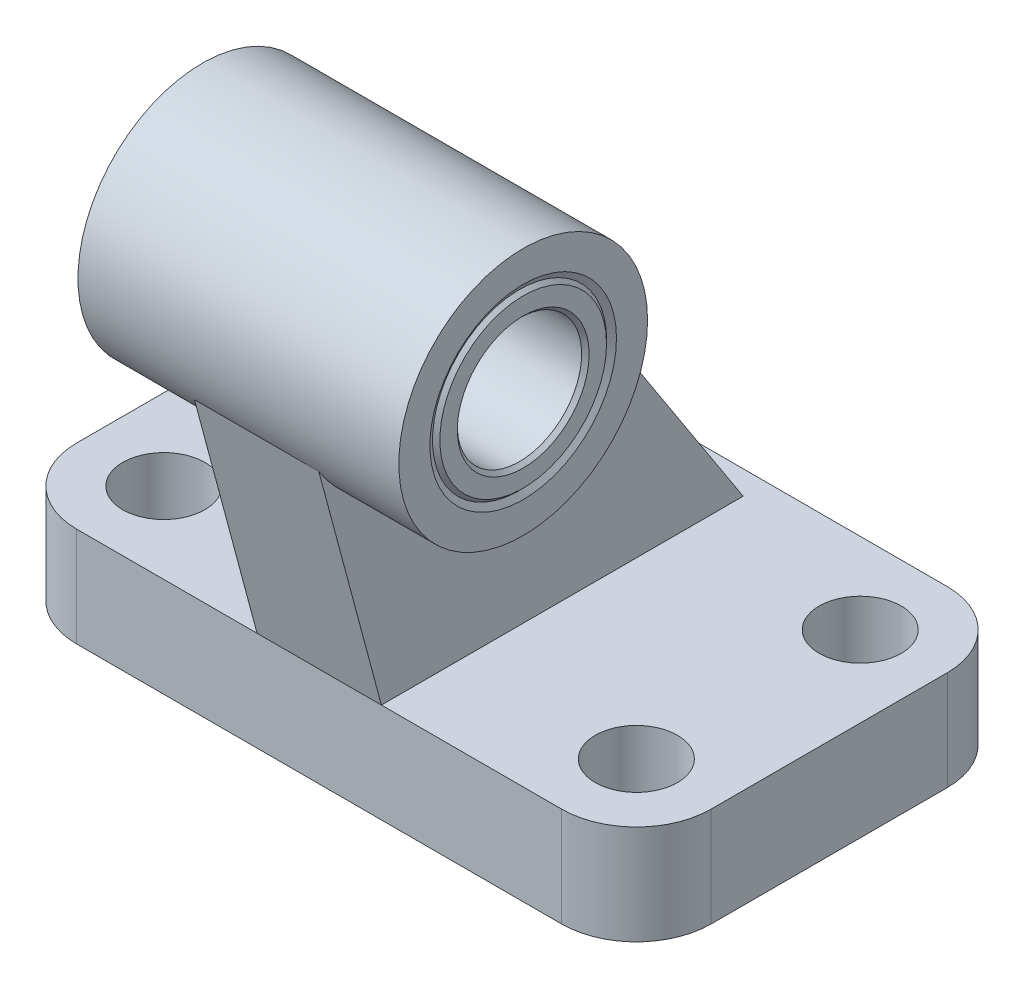
SolidWorks part; units mm, degrees
ref_plane "Front Plane" through (0, 0, 0) normal (0, 0, 1) x (1, 0, 0)
ref_plane "Top Plane" through (0, 0, 0) normal (0, 1, 0) x (1, 0, 0)
ref_plane "Right Plane" through (0, 0, 0) normal (1, 0, 0) x (0, 0, -1)
ref_plane "Plane1" through (0, 0, 0) normal (0, 1, 0) x (1, 0, 0)
sketch "Sketch1" plane through (0, 0, 0) normal (0, 1, 0) x (1, 0, 0)
  line L0 (-19.5, -15.5) -> (19.5, -15.5)
  line L1 (25.5, -9.5) -> (25.5, 9.5)
  line L2 (19.5, 15.5) -> (-19.5, 15.5)
  line L3 (-25.5, 9.5) -> (-25.5, -9.5)
  arc A0 (-25.5, -9.5) -> (-19.5, -15.5) centre (-19.5, -9.5) ccw
  arc A1 (19.5, -15.5) -> (25.5, -9.5) centre (19.5, -9.5) ccw
  arc A2 (25.5, 9.5) -> (19.5, 15.5) centre (19.5, 9.5) ccw
  arc A3 (-19.5, 15.5) -> (-25.5, 9.5) centre (-19.5, 9.5) ccw
extrude "Boss-Extrude1" add sketch "Sketch1" along normal blind 8
ref_plane "Plane2" through (0, 0, 0) normal (1, 0, 0) x (0, 0, -1)
sketch "Sketch2" plane through (0, 0, 0) normal (1, 0, 0) x (0, 0, -1)
  line L0 (-21.2655, 29.5173) -> (-15.5, 8)
  line L1 (-15.5, 8) -> (13.5858, 8)
  line L2 (13.5858, 8) -> (-3.4822, 34.2823)
  line L3 (-3.4822, 34.2823) -> (-21.2655, 29.5173)
extrude "Boss-Extrude2" add sketch "Sketch2" against normal blind 5 and the other way blind 5
ref_plane "Plane3" through (0, 0, 0) normal (1, 0, 0) x (0, 0, -1)
sketch "Sketch3" plane through (0, 0, 0) normal (1, 0, 0) x (0, 0, -1)
  circle A0 centre (-12, 32) radius 10
extrude "Boss-Extrude3" add sketch "Sketch3" against normal blind 12.9 and the other way blind 12.9
ref_plane "Plane4" through (0, 0, 9) normal (0, 0, 1) x (1, 0, 0)
sketch "Sketch4" plane through (0, 0, 9) normal (0, 0, 1) x (1, 0, 0)
  line L0 (-19, 0) -> (-22.3, 0)
  line L1 (-22.3, 0) -> (-22.3, 8)
  line L2 (-22.3, 8) -> (-19, 8)
  line L3 (-19, 8) -> (-19, 0)
  line L4 (-19, 8) -> (-19, 0) construction
revolve "Cut-Revolve1" cut sketch "Sketch4" angle 360 about L4
ref_plane "Plane5" through (0, 0, 9) normal (0, 0, 1) x (1, 0, 0)
sketch "Sketch5" plane through (0, 0, 9) normal (0, 0, 1) x (1, 0, 0)
  line L0 (19, 0) -> (15.7, 0)
  line L1 (15.7, 0) -> (15.7, 8)
  line L2 (15.7, 8) -> (19, 8)
  line L3 (19, 8) -> (19, 0)
  line L4 (19, 8) -> (19, 0) construction
revolve "Cut-Revolve2" cut sketch "Sketch5" angle 360 about L4
ref_plane "Plane6" through (0, 0, -9) normal (0, 0, 1) x (1, 0, 0)
sketch "Sketch6" plane through (0, 0, -9) normal (0, 0, 1) x (1, 0, 0)
  line L0 (-19, 0) -> (-22.3, 0)
  line L1 (-22.3, 0) -> (-22.3, 8)
  line L2 (-22.3, 8) -> (-19, 8)
  line L3 (-19, 8) -> (-19, 0)
  line L4 (-19, 8) -> (-19, 0) construction
revolve "Cut-Revolve3" cut sketch "Sketch6" angle 360 about L4
ref_plane "Plane7" through (0, 0, -9) normal (0, 0, 1) x (1, 0, 0)
sketch "Sketch7" plane through (0, 0, -9) normal (0, 0, 1) x (1, 0, 0)
  line L0 (19, 0) -> (15.7, 0)
  line L1 (15.7, 0) -> (15.7, 8)
  line L2 (15.7, 8) -> (19, 8)
  line L3 (19, 8) -> (19, 0)
  line L4 (19, 8) -> (19, 0) construction
revolve "Cut-Revolve4" cut sketch "Sketch7" angle 360 about L4
ref_plane "Plane8" through (0, 0, 12) normal (0, 0, 1) x (1, 0, 0)
sketch "Sketch8" plane through (0, 0, 12) normal (0, 0, 1) x (1, 0, 0)
  line L0 (-12.9, 32) -> (-12.9, 39.5)
  line L1 (-12.9, 39.5) -> (-12.6113, 39)
  line L2 (-12.6113, 39) -> (12.6113, 39)
  line L3 (12.6113, 39) -> (12.9, 39.5)
  line L4 (12.9, 39.5) -> (12.9, 32)
  line L5 (12.9, 32) -> (-12.9, 32)
  line L6 (12.9, 32) -> (-12.9, 32) construction
revolve "Cut-Revolve5" cut sketch "Sketch8" angle 360 about L6
ref_plane "Plane9" through (0, 0, 12) normal (0, 0, 1) x (1, 0, 0)
sketch "Sketch9" plane through (0, 0, 12) normal (0, 0, 1) x (1, 0, 0)
  line L0 (-12.9, 37.3) -> (-12.6, 37)
  line L1 (-12.6, 37) -> (12.6, 37)
  line L2 (12.6, 37) -> (12.9, 37.3)
  line L3 (12.9, 37.3) -> (12.9, 38.7)
  line L4 (12.9, 38.7) -> (12.6, 39)
  line L5 (12.6, 39) -> (-12.6, 39)
  line L6 (-12.6, 39) -> (-12.9, 38.7)
  line L7 (-12.9, 38.7) -> (-12.9, 37.3)
  line L8 (12.9, 32) -> (-12.9, 32) construction
revolve "Revolve1" add sketch "Sketch9" angle 360 about L8
